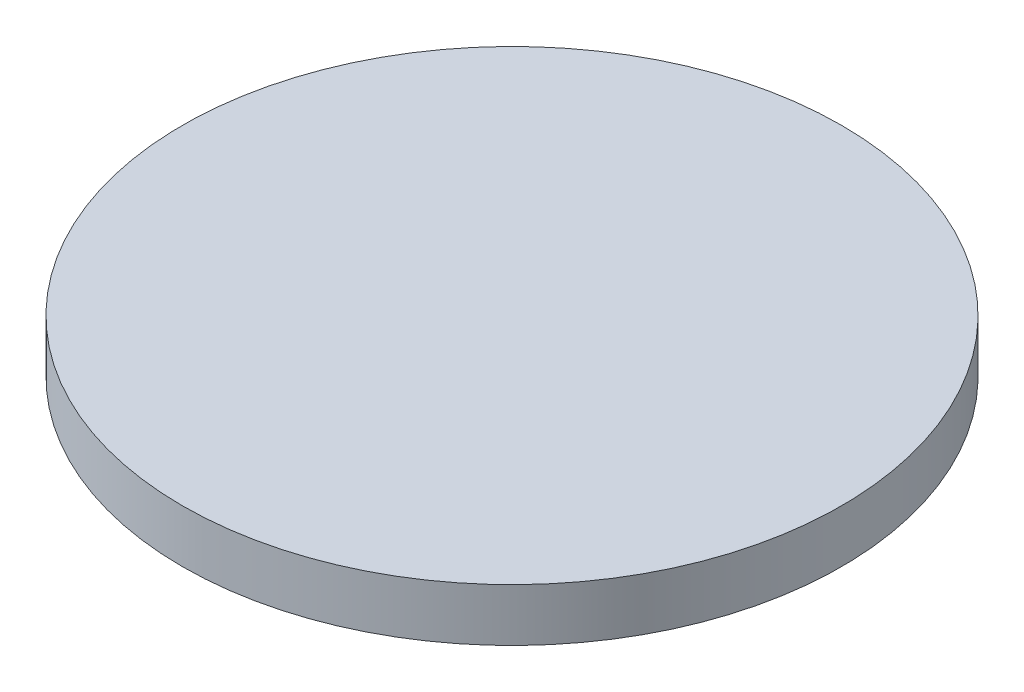
SolidWorks part; units mm, degrees
ref_plane "前视基准面" through (0, 0, 0) normal (0, 0, 1) x (1, 0, 0)
ref_plane "上视基准面" through (0, 0, 0) normal (0, 1, 0) x (1, 0, 0)
ref_plane "右视基准面" through (0, 0, 0) normal (1, 0, 0) x (0, 0, -1)
sketch "草图1" plane through (0, 0, 0) normal (0, 1, 0) x (1, 0, 0)
  circle A0 centre (0, 0) radius 12.5
  dimension "D1" = 25
extrude "凸台-拉伸1" add sketch "草图1" along normal blind 2
